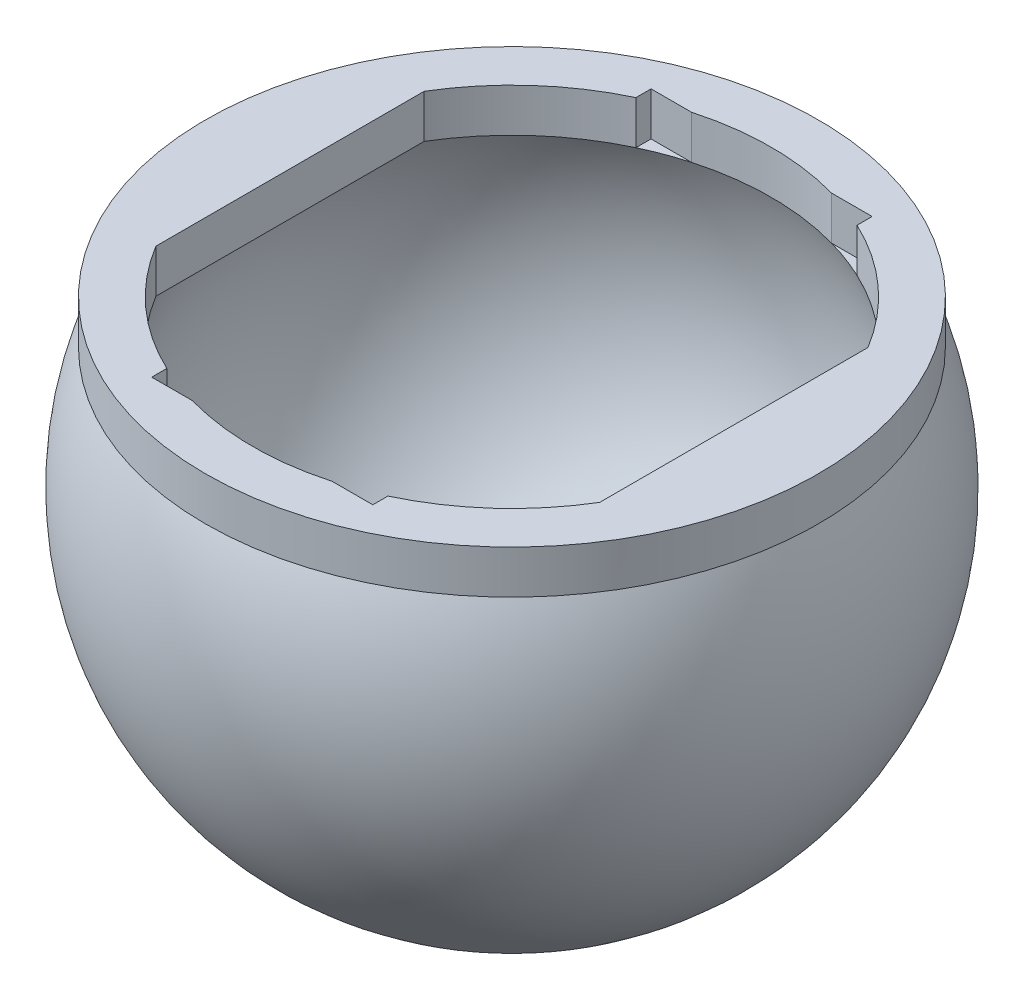
SolidWorks part; units mm, degrees
ref_plane "Front Plane" through (0, 0, 0) normal (0, 0, 1) x (1, 0, 0)
ref_plane "Top Plane" through (0, 0, 0) normal (0, 1, 0) x (1, 0, 0)
ref_plane "Right Plane" through (0, 0, 0) normal (1, 0, 0) x (0, 0, -1)
sketch "Sketch1" plane through (0, 0, 0) normal (0, 0, 1) x (1, 0, 0)
  line L0 (-17.6635, 7) -> (17.6635, 7)
  line L1 (0, -16.5) -> (0, -19)
  line L2 (0, -16.5) -> (0, 27.758) construction
  circle A0 centre (0, 0) radius 16.5
  circle A1 centre (0, 0) radius 19
  dimension "D1" = 16.5
  dimension "D2" = 2.5
  dimension "D3" = 7
revolve "Revolve2" add sketch "Sketch1" angle 360 about L2
sketch "Sketch2" plane through (0, 7, 0) normal (0, 1, 0) x (1, 0, 0)
  line L1 (12.7867, 12.186) -> (-12.7867, 12.186)
  line L2 (12.7867, 12.186) -> (12.7867, -12.186)
  line L3 (12.7867, -12.186) -> (-12.7867, -12.186)
  line L4 (-12.7867, 12.186) -> (-12.7867, -12.186)
  circle A0 centre (0, 0) radius 17.6635
  circle M6 centre (0, 0) radius 17.6635
  circle M7 centre (0, 0) radius 14.9416
extrude "Boss-Extrude1" add sketch "Sketch2" along normal blind 2.5 contours L2 M6 M7 | L2 M7 | L4 M6 M7 | L4 M7 | L1 M6 M7 | L2 L1 M7 | L1 L4 M7 | L4 L3 M7 | L3 L2 M7 | L3 M6 M7
sketch "Sketch3" plane through (0, 9.5, 0) normal (0, 1, 0) x (1, 0, 0)
  line L0 (-6.37, -14.3875) -> (-6.37, -13.5157)
  line L2 (-6.37, -14.3875) -> (-4.0311, -14.3875)
  line L3 (0, 0) -> (-16.505, 0) construction
  line L4 (-6.37, 14.3875) -> (-6.37, 13.5157)
  line L5 (-6.37, 14.3875) -> (-4.0311, 14.3875)
  line L6 (0, 21.2873) -> (0, -21.7345) construction
  line L7 (6.37, -14.3875) -> (6.37, -13.5157)
  line L8 (6.37, -14.3875) -> (4.0311, -14.3875)
  line L9 (6.37, 14.3875) -> (6.37, 13.5157)
  line L10 (6.37, 14.3875) -> (4.0311, 14.3875)
  circle A0 centre (0, 0) radius 14.9416
  arc A1 (-12.7867, -7.7298) -> (12.7867, -7.7298) centre (0, 0) ccw construction
  arc M3 (-12.7867, 7.7298) -> (12.7867, 7.7298) centre (0, 0) cw
  arc M5 (12.7867, -7.7298) -> (-12.7867, -7.7298) centre (0, 0) cw
extrude "Cut-Extrude1" cut sketch "Sketch3" against normal blind 2.5 contours L5 L4 M3 | L9 L10 M3 | L8 L7 M5 | L0 L2 M5
